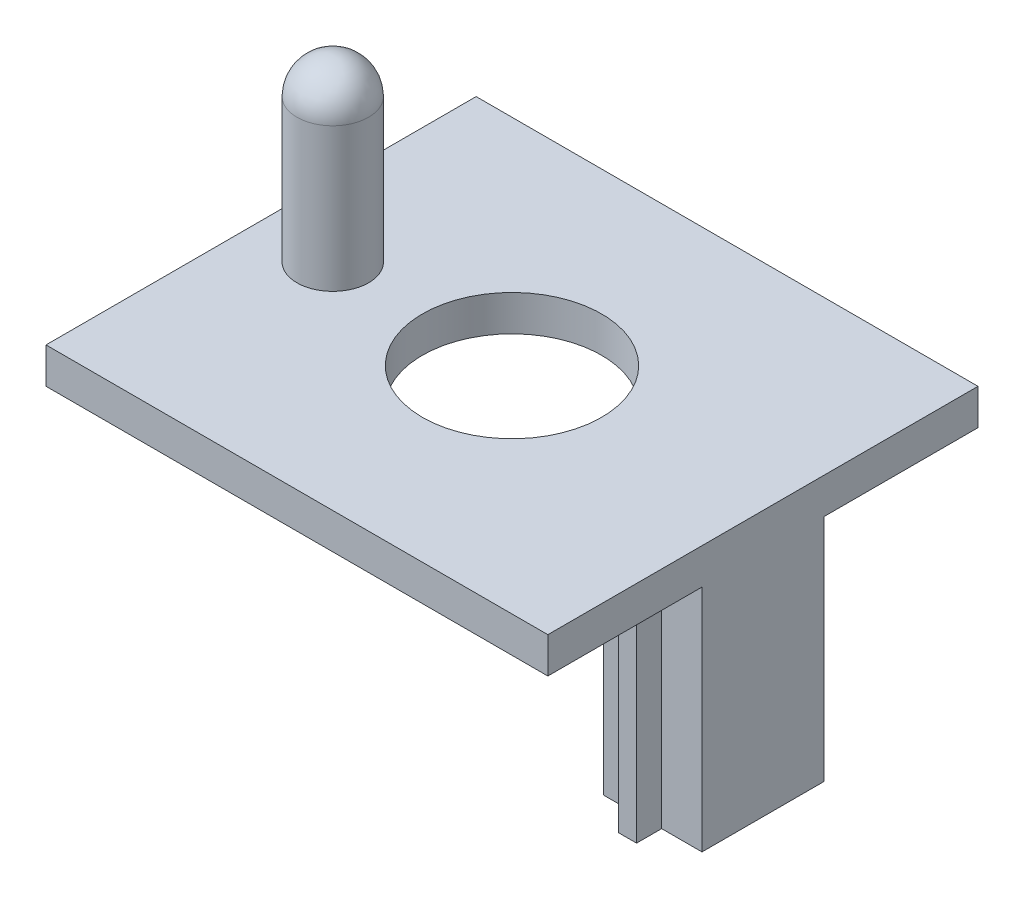
SolidWorks part; units mm, degrees
ref_plane "Alzado" through (0, 0, 0) normal (0, 0, 1) x (1, 0, 0)
ref_plane "Planta" through (0, 0, 0) normal (0, 1, 0) x (1, 0, 0)
ref_plane "Vista lateral" through (0, 0, 0) normal (1, 0, 0) x (0, 0, -1)
sketch "Croquis1" plane through (0, 0, 0) normal (0, 1, 0) x (1, 0, 0)
  line L1 (-35, 30) -> (35, 30)
  line L2 (-35, 30) -> (-35, -30)
  line L3 (-35, -30) -> (35, -30)
  line L4 (35, 30) -> (35, -30)
  line L5 (-35, 30) -> (35, -30) construction
  line L6 (-35, -30) -> (35, 30) construction
  circle A0 centre (0, 0) radius 12.5
  point P0 (0, 0)
  dimension "D3" = 25
  dimension "D1" = 60
  dimension "D2" = 70
extrude "Saliente-Extruir1" add sketch "Croquis1" along normal blind 5
sketch "Croquis2" plane through (0, 0, 0) normal (0, -1, 0) x (1, 0, 0)
  line L0 (35, 30) -> (35, -30) construction
  line L1 (-21.25, 21.25) -> (21.25, 21.25)
  line L2 (-21.25, 21.25) -> (-21.25, -21.25)
  line L3 (-21.25, -21.25) -> (21.25, -21.25)
  line L4 (21.25, 21.25) -> (21.25, -21.25)
  line L5 (-21.25, 21.25) -> (21.25, -21.25) construction
  line L6 (-21.25, -21.25) -> (21.25, 21.25) construction
  line L7 (21.25, 8.5) -> (35, 8.5)
  line L8 (21.25, 8.5) -> (21.25, -8.5)
  line L9 (21.25, -8.5) -> (35, -8.5)
  line L10 (35, 8.5) -> (35, -8.5)
  line L11 (21.25, 8.5) -> (35, -8.5) construction
  line L12 (21.25, -8.5) -> (35, 8.5) construction
  line L14 (26.875, 12) -> (29.375, 12)
  line L15 (26.875, 12) -> (26.875, -12)
  line L16 (26.875, -12) -> (29.375, -12)
  line L17 (29.375, 12) -> (29.375, -12)
  line L18 (26.875, 12) -> (29.375, -12) construction
  line L19 (26.875, -12) -> (29.375, 12) construction
  point P0 (0, 0)
  point P6 (28.125, 0)
  point P13 (28.125, 0)
  line M13 (35, -30) -> (35, 30)
  dimension "D1" = 42.5
  dimension "D2" = 42.5
  dimension "D3" = 17
  dimension "D4" = 24
  dimension "D5" = 2.5
extrude "Saliente-Extruir2" add sketch "Croquis2" along normal blind 32 contours L7 L17 L9 M13 | L17 L7 L15 L9 | L17 L14 L15 L7 | L15 L7 L4 L9 | L17 L9 L15 L16
sketch "Croquis3" plane through (0, 5, 0) normal (0, 1, 0) x (1, 0, 0)
  circle A0 centre (-25, 0) radius 5
  point P2 (0, 0)
  dimension "D1" = 10
  dimension "D2" = 25
extrude "Saliente-Extruir3" add sketch "Croquis3" along normal blind 25
fillet "Redondeo1" radius 5 1 edges at (-25, 30, 5)
